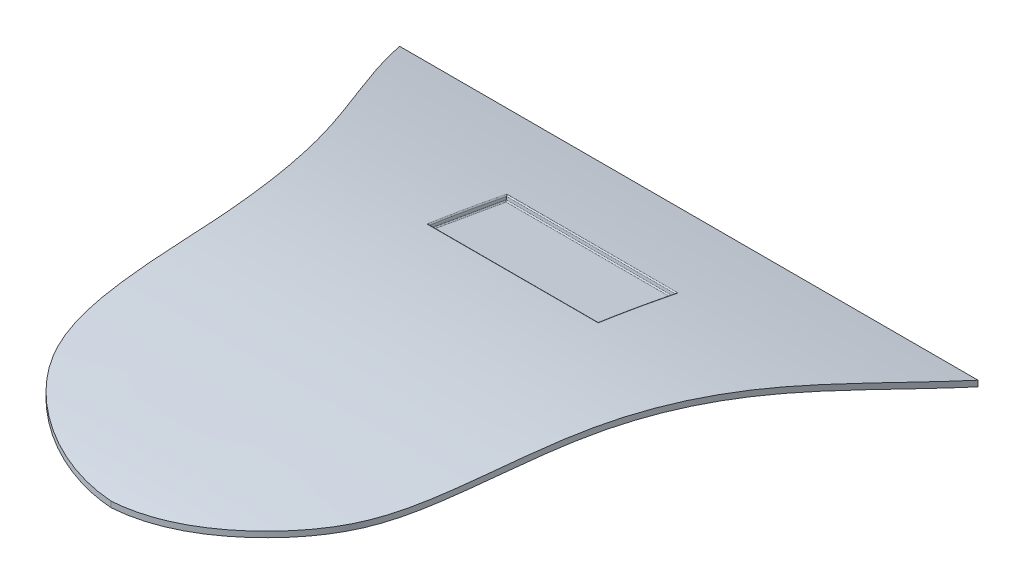
SolidWorks part; units mm, degrees
ref_plane "Plan de face" through (0, 0, 0) normal (0, 0, 1) x (1, 0, 0)
ref_plane "Plan de dessus" through (0, 0, 0) normal (0, 1, 0) x (1, 0, 0)
ref_plane "Plan de droite" through (0, 0, 0) normal (1, 0, 0) x (0, 0, -1)
sketch "Esquisse1" plane through (0, 0, 0) normal (0, 1, 0) x (1, 0, 0)
  line L0 (-25.6413, -201) -> (25.6413, -201)
  line L2 (0, 0) -> (0, -258.4333) construction
  spline S0 degree 3 poles (25.6413, -201) (23.961, -205.2785) (19.3057, -212.7731) (16.083, -224.9547) (15.7134, -235.2412) (14.0804, -243.7382) (9.462, -248.8913) (4.5652, -251.5054) (1.3811, -252.1339) (0, -252.2146) knots 0 0 0 0 0.22317 0.426641 0.602759 0.727119 0.836395 0.926386 0.9931 0.9931 0.9931 0.9931
  spline S1 degree 3 poles (-25.6413, -201) (-23.961, -205.2785) (-19.3057, -212.7731) (-16.083, -224.9547) (-15.7134, -235.2412) (-14.0804, -243.7382) (-9.462, -248.8913) (-4.5652, -251.5054) (-1.3811, -252.1339) (0, -252.2146) knots 0 0 0 0 0.22317 0.426641 0.602759 0.727119 0.836395 0.926386 0.9931 0.9931 0.9931 0.9931
  point P24 (0, -201)
extrude "Extrusion1" add sketch "Esquisse1" along normal blind 10
sketch "Esquisse2" plane through (0, 0, 0) normal (1, 0, 0) x (0, 0, -1)
  line L0 (-252.7875, 6.044) -> (-253.1711, 11.3056)
  line L1 (-253.1711, 11.3056) -> (-199.8829, 11.3056)
  line L2 (-199.8829, 11.3056) -> (-200.8797, 2.6417)
  line L3 (-252.6759, 5.5566) -> (-252.6759, -1.4895)
  line L4 (-252.6759, -1.4895) -> (-199.2556, -1.4895)
  line L5 (-199.2556, -1.4895) -> (-201, 2.1564)
  spline S0 degree 3 poles (-201, 2.1564) (-206.9849, 3.6398) (-216.1883, 5.6053) (-228.641, 6.5935) (-236.9333, 6.6832) (-244.92, 6.4022) (-249.8172, 6.211) (-252.6759, 5.5566) knots 0 0 0 0 0.355293 0.539869 0.718237 0.832338 1 1 1 1
  spline S3 degree 1 poles (-200.8797, 2.6417) (-252.7875, 6.044) knots 0 0 1 1 construction
  spline S4 degree 3 poles (-200.8797, 2.6417) (-205.1067, 3.6894) (-211.4834, 5.1169) (-220.1216, 6.3823) (-226.645, 6.9349) (-233.1814, 7.1663) (-238.6301, 7.1192) (-242.9754, 6.9688) (-246.2361, 6.8575) (-249.511, 6.6376) (-251.7095, 6.2907) (-252.7875, 6.044) knots 0 0 0 0 0.25 0.375 0.5 0.625 0.75 0.8125 0.875 0.9375 1 1 1 1
  dimension "D1" = 0.5
extrude "Extrusion2" cut sketch "Esquisse2" against normal mid plane 60
sketch "Esquisse3" plane through (0, 0, 0) normal (0, 1, 0) x (1, 0, 0)
  line L0 (-26.8771, -214) -> (31.1143, -214) construction
  line L1 (-25.6413, -201) -> (25.6413, -201) construction
  dimension "D1" = 13
ref_plane "Plan1" through (0, -36.5962, 6.4529) normal (0, -0.9848, 0.1736) x (1, 0, 0)
ref_plane "Plan2" through (0, -31.4752, 5.5499) normal (0, -0.9848, 0.1736) x (1, 0, 0)
sketch "Esquisse4" plane through (0, -31.4752, 5.5499) normal (0, -0.9848, 0.1736) x (1, 0, 0)
  line L1 (-8.5, 214.7489) -> (8.5, 214.7489)
  line L2 (-8.5, 214.7489) -> (-8.5, 206.7489)
  line L3 (-8.5, 206.7489) -> (8.5, 206.7489)
  line L4 (8.5, 214.7489) -> (8.5, 206.7489)
  line L7 (-26.8771, 210.7489) -> (31.1143, 210.7489) construction
  dimension "D1" = 17
  dimension "D2" = 8
  dimension "D3" = 4
  dimension "D4" = 8.5
extrude "Extrusion3" add sketch "Esquisse4" along normal blind 0.8
ref_plane "Plan3" through (0, -31.0934, 5.4826) normal (0, -0.9848, 0.1736) x (1, 0, 0)
sketch "Esquisse5" plane through (0, -31.0934, 5.4826) normal (0, -0.9848, 0.1736) x (1, 0, 0)
  line L0 (-26.8771, 210.7489) -> (31.1143, 210.7489) construction
  line L1 (7.5, 214.2489) -> (-7.5, 214.2489)
  line L2 (7.5, 214.2489) -> (7.5, 207.2489)
  line L3 (7.5, 207.2489) -> (-7.5, 207.2489)
  line L4 (-7.5, 214.2489) -> (-7.5, 207.2489)
  dimension "D1" = 15
  dimension "D2" = 7
  dimension "D3" = 3.5
  dimension "D4" = 7.5
extrude "Extrusion7" cut sketch "Esquisse5" along normal blind 0.7
fillet "Congé2" radius 0.1 8 edges at (0, 4.2056, 209.7044) (7.5, 4.8134, 213.1513) (-7.5, 4.8134, 213.1513) (0, 5.4211, 216.5981) (0, 4.6267, 209.6302) (0, 5.84, 216.5242)
fillet "Congé5" radius 0.1 11 edges at (-8.5, 3.8363, 209.2619) (8.5, 3.8363, 209.2619) (0, 4.034, 209.227) (8.5, 5.2241, 217.1406) (8.5, 4.3332, 213.2359) (0, 3.6386, 209.2967) (-8.5, 5.2241, 217.1406) (0, 5.0277, 217.1752) (0, 5.4204, 217.106)
